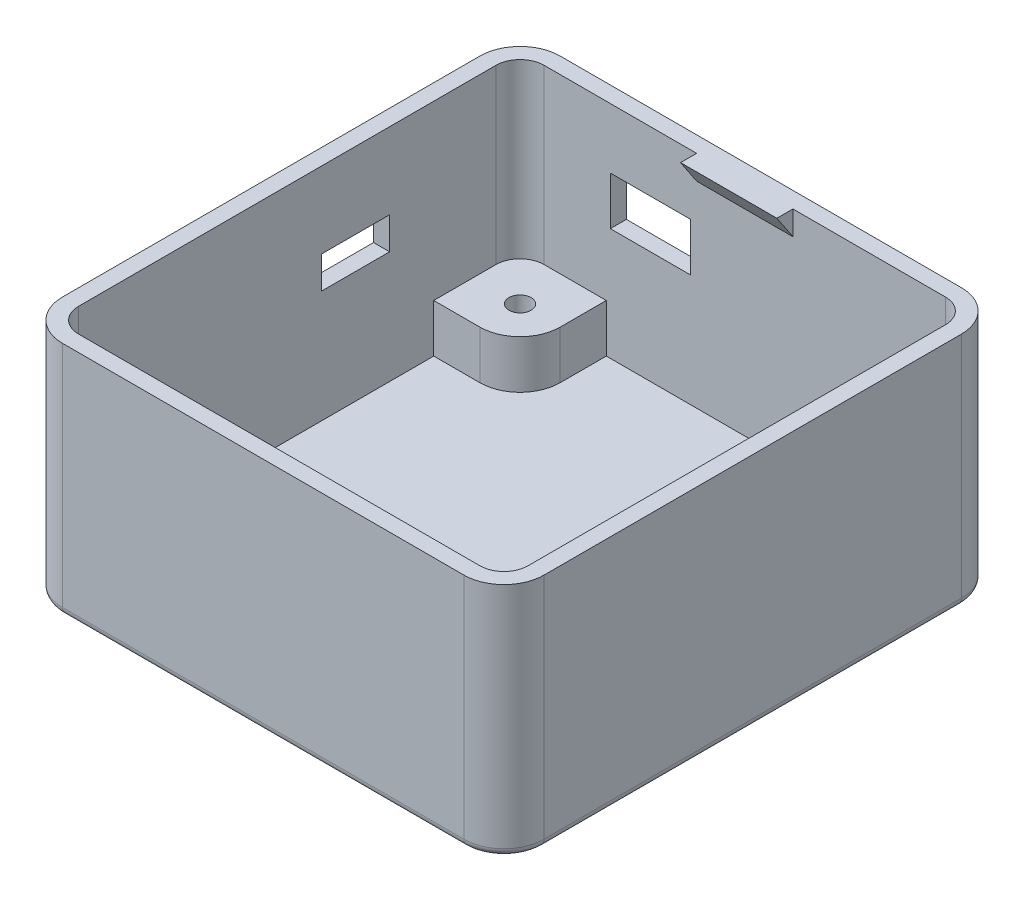
SolidWorks part; units mm, degrees
ref_plane "Front Plane" through (0, 0, 0) normal (0, 0, 1) x (1, 0, 0)
ref_plane "Top Plane" through (0, 0, 0) normal (0, 1, 0) x (1, 0, 0)
ref_plane "Right Plane" through (0, 0, 0) normal (1, 0, 0) x (0, 0, -1)
sketch "Sketch1" plane through (0, 0, 0) normal (0, 1, 0) x (1, 0, 0)
  line L1 (-25, -31) -> (25, -31)
  line L2 (-30, -26) -> (-30, 26)
  line L3 (-25, 31) -> (25, 31)
  line L4 (30, -26) -> (30, 26)
  line L5 (-30, -31) -> (30, 31) construction
  line L6 (-30, 31) -> (30, -31) construction
  arc A0 (25, 31) -> (30, 26) centre (25, 26) cw
  arc A1 (30, -26) -> (25, -31) centre (25, -26) cw
  arc A2 (-25, -31) -> (-30, -26) centre (-25, -26) cw
  arc A3 (-30, 26) -> (-25, 31) centre (-25, 26) cw
  point P0 (0, 0)
  dimension "D3" = 5
  dimension "D1" = 62
  dimension "D2" = 60
extrude "Boss-Extrude1" add sketch "Sketch1" along normal blind 29.5
sketch "Sketch2" plane through (0, 29.5, 0) normal (0, 1, 0) x (1, 0, 0)
  line L4 (25, 31) -> (-25, 31)
  line L5 (-30, 26) -> (-30, -26)
  line L6 (-25, -31) -> (25, -31)
  line L7 (30, -26) -> (30, 26)
  line L8 (25, 31) -> (-25, 31)
  line L9 (-30, 26) -> (-30, -26)
  line L10 (-25, -31) -> (25, -31)
  line L11 (30, -26) -> (30, 26)
  line L16 (25, 29) -> (-25, 29)
  line L17 (-28, 26) -> (-28, -26)
  line L18 (-25, -29) -> (25, -29)
  line L19 (28, -26) -> (28, 26)
  line L20 (25, 29) -> (-25, 29)
  line L21 (-28, 26) -> (-28, -26)
  line L22 (-25, -29) -> (25, -29)
  line L23 (28, -26) -> (28, 26)
  arc A4 (30, 26) -> (25, 31) centre (25, 26) ccw
  arc A5 (-25, 31) -> (-30, 26) centre (-25, 26) ccw
  arc A6 (-30, -26) -> (-25, -31) centre (-25, -26) ccw
  arc A7 (25, -31) -> (30, -26) centre (25, -26) ccw
  arc A8 (30, 26) -> (25, 31) centre (25, 26) ccw
  arc A9 (-25, 31) -> (-30, 26) centre (-25, 26) ccw
  arc A10 (-30, -26) -> (-25, -31) centre (-25, -26) ccw
  arc A11 (25, -31) -> (30, -26) centre (25, -26) ccw
  arc A16 (28, 26) -> (25, 29) centre (25, 26) ccw
  arc A17 (-25, 29) -> (-28, 26) centre (-25, 26) ccw
  arc A18 (-28, -26) -> (-25, -29) centre (-25, -26) ccw
  arc A19 (25, -29) -> (28, -26) centre (25, -26) ccw
  arc A20 (28, 26) -> (25, 29) centre (25, 26) ccw
  arc A21 (-25, 29) -> (-28, 26) centre (-25, 26) ccw
  arc A22 (-28, -26) -> (-25, -29) centre (-25, -26) ccw
  arc A23 (25, -29) -> (28, -26) centre (25, -26) ccw
  dimension "D1" = 0
  dimension "D2" = 2
extrude "Cut-Extrude1" cut sketch "Sketch2" against normal offset from surface (27.5 mm away) 2 contours L22 A23 L23 A20 L20 A21 L21 A22 up to face at (0, 0, 0)
sketch "Sketch4" plane through (0, 2, 0) normal (0, 1, 0) x (1, 0, 0)
  line L0 (28, 18.25) -> (22.25, 18.25)
  line L1 (28, -26) -> (28, 26) construction
  line L2 (17.25, 23.25) -> (17.25, 29)
  line L3 (25, 29) -> (-25, 29) construction
  line L4 (28, -18.25) -> (22.25, -18.25)
  line L5 (17.25, -23.25) -> (17.25, -29)
  line L6 (-25, -29) -> (25, -29) construction
  line L7 (-17.25, -29) -> (-17.25, -23.25)
  line L8 (-22.25, -18.25) -> (-28, -18.25)
  line L9 (-28, 26) -> (-28, -26) construction
  line L10 (-28, 18.25) -> (-22.25, 18.25)
  line L11 (-17.25, 23.25) -> (-17.25, 29)
  line L14 (-25, -29) -> (25, -29)
  line L15 (28, -26) -> (28, 26)
  line L16 (25, 29) -> (-25, 29)
  line L17 (-28, 26) -> (-28, -26)
  line L18 (-25, -29) -> (25, -29)
  line L19 (28, -26) -> (28, 26)
  line L20 (25, 29) -> (-25, 29)
  line L21 (-28, 26) -> (-28, -26)
  arc A4 (25, -29) -> (28, -26) centre (25, -26) ccw
  arc A5 (28, 26) -> (25, 29) centre (25, 26) ccw
  arc A6 (-25, 29) -> (-28, 26) centre (-25, 26) ccw
  arc A7 (-28, -26) -> (-25, -29) centre (-25, -26) ccw
  arc A8 (25, -29) -> (28, -26) centre (25, -26) ccw
  arc A9 (28, 26) -> (25, 29) centre (25, 26) ccw
  arc A10 (-25, 29) -> (-28, 26) centre (-25, 26) ccw
  arc A11 (-28, -26) -> (-25, -29) centre (-25, -26) ccw
  arc A12 (17.25, -23.25) -> (22.25, -18.25) centre (22.25, -23.25) cw
  arc A13 (-17.25, -23.25) -> (-22.25, -18.25) centre (-22.25, -23.25) ccw
  arc A14 (22.25, 18.25) -> (17.25, 23.25) centre (22.25, 23.25) cw
  arc A15 (-22.25, 18.25) -> (-17.25, 23.25) centre (-22.25, 23.25) ccw
  circle A16 centre (-22.25, 23.25) radius 1.375
  circle A17 centre (22.25, 23.25) radius 1.375
  circle A18 centre (22.25, -23.25) radius 1.375
  circle A19 centre (-22.25, -23.25) radius 1.375
  point P43 (-17.25, 26.125)
  point P44 (17.25, 26.125)
  point P47 (17.25, -26.125)
  point P48 (-17.25, -26.125)
  line M17 (-25, -29) -> (25, -29)
  arc M18 (25, -29) -> (28, -26) centre (25, -26) ccw
  line M19 (28, -26) -> (28, 26)
  arc M20 (28, 26) -> (25, 29) centre (25, 26) ccw
  line M21 (25, 29) -> (-25, 29)
  arc M22 (-25, 29) -> (-28, 26) centre (-25, 26) ccw
  line M23 (-28, 26) -> (-28, -26)
  arc M24 (-28, -26) -> (-25, -29) centre (-25, -26) ccw
  dimension "D2" = 2.75
  dimension "D3" = 44.5
  dimension "D4" = 5
  dimension "D1" = 0
extrude "Boss-Extrude2" add sketch "Sketch4" along normal blind 6 contours L10 A15 L11 A16 M21 M22 M23 | A14 L0 L2 A17 M19 M20 M21 | L7 A13 L8 A19 M23 M24 M17 | A12 L5 L4 A18 M17 M18 M19
sketch "Sketch5" plane through (-30, 0, 0) normal (-1, 0, 0) x (0, 0, 1)
  line L2 (-21.875, 8) -> (-24.625, 8) construction
  line L3 (-12.75, 16) -> (-4.25, 16)
  line L4 (-26, 0) -> (26, 0)
  line L5 (26, 0) -> (26, 29.5)
  line L6 (26, 29.5) -> (-26, 29.5)
  line L7 (-26, 29.5) -> (-26, 0)
  line L8 (-26, 0) -> (26, 0)
  line L9 (26, 0) -> (26, 29.5)
  line L10 (26, 29.5) -> (-26, 29.5)
  line L11 (-26, 29.5) -> (-26, 0)
  line L12 (-12.75, 16) -> (-12.75, 20)
  line L13 (-12.75, 20) -> (-4.25, 20)
  line L14 (-4.25, 16) -> (-4.25, 20)
  line L15 (-21.875, 8) -> (-24.625, 8)
  point P2 (-23.25, 8)
  point P4 (-12.75, 18)
  dimension "D2" = 4
  dimension "D3" = 8.5
  dimension "D4" = 8
  dimension "D5" = 10.5
  dimension "D1" = 0
extrude "Cut-Extrude2" cut sketch "Sketch5" against normal up to next contours L3 L14 L13 L12
sketch "Sketch6" plane through (0, 0, -31) normal (0, 0, -1) x (-1, 0, 0)
  line L0 (23.625, 8) -> (20.875, 8) construction
  line L1 (23.625, 8) -> (20.875, 8)
  line L3 (16.75, 16) -> (6.75, 16)
  line L4 (-25, 0) -> (25, 0)
  line L5 (25, 0) -> (25, 29.5)
  line L6 (25, 29.5) -> (-25, 29.5)
  line L7 (-25, 29.5) -> (-25, 0)
  line L8 (-25, 0) -> (25, 0)
  line L9 (25, 0) -> (25, 29.5)
  line L10 (25, 29.5) -> (-25, 29.5)
  line L11 (-25, 29.5) -> (-25, 0)
  line L12 (16.75, 16) -> (16.75, 22)
  line L13 (16.75, 22) -> (6.75, 22)
  line L14 (6.75, 16) -> (6.75, 22)
  point P10 (22.25, 8)
  dimension "D2" = 6
  dimension "D3" = 10
  dimension "D4" = 8
  dimension "D5" = 5.5
  dimension "D1" = 0
extrude "Cut-Extrude3" cut sketch "Sketch6" against normal up to next contours L14 L3 L12 L13
ref_plane "Plane1" through (0, 0, 0) normal (-1, 0, 0) x (0, 0, 1)
ref_plane "Plane2" through (-6, 0, 0) normal (-1, 0, 0) x (0, 0, 1)
sketch "Sketch7" plane through (-6, 0, 0) normal (-1, 0, 0) x (0, 0, 1)
  line L3 (-29, 8) -> (-29, 29.5) construction
  line L4 (-29, 8) -> (-29, 29.5)
  line L5 (-29, 29.5) -> (-27, 29.5)
  line L6 (-27, 29.5) -> (-29, 26.5)
  dimension "D1" = 2
  dimension "D2" = 3
extrude "Boss-Extrude3" add sketch "Sketch7" against normal blind 12 contours L6 L5 L4
fillet "Fillet1" radius 1 8 edges at (-30, 0, 0) (-28.5355, 0, -29.5355) (0, 0, -31) (28.5355, 0, -29.5355) (30, 0, 0) (28.5355, 0, 29.5355) (0, 0, 31) (-28.5355, 0, 29.5355)
